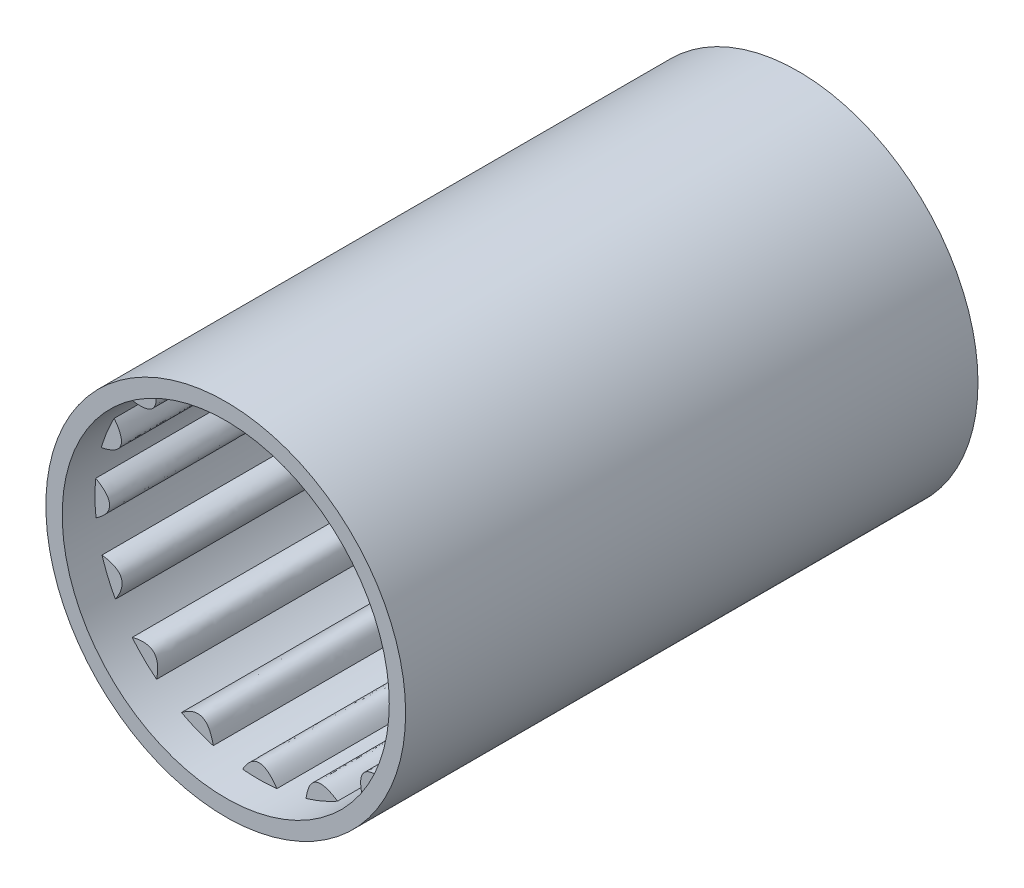
SolidWorks part; units mm, degrees
ref_plane "Front Plane" through (0, 0, 0) normal (0, 0, 1) x (1, 0, 0)
ref_plane "Top Plane" through (0, 0, 0) normal (0, 1, 0) x (1, 0, 0)
ref_plane "Right Plane" through (0, 0, 0) normal (1, 0, 0) x (0, 0, -1)
sketch "Sketch1" plane through (0, 0, 0) normal (0, 0, 1) x (1, 0, 0)
  circle A0 centre (0, 0) radius 11
  circle A1 centre (0, 0) radius 10
  dimension "D1" = 20
  dimension "22" = 22
extrude "Boss-Extrude1" add sketch "Sketch1" along normal blind 35
sketch "Sketch2" plane through (0, 0, 0) normal (0, 0, -1) x (-1, 0, 0)
  circle A0 centre (0, 0) radius 10 construction
  spline S0 degree 2 poles (-1.1281, -9.9362) (-0.0088, -8.2617) (0.9751, -9.9523) knots 0 0 0 1 1 1
  spline S1 degree 2 poles (-1.1281, -9.9362) (-0.0769, -10.0552) (0.9751, -9.9523) knots 0 0 0 1 1 1
  spline S2 degree 2 poles (-4.8446, -8.7481) (-3.1698, -7.6295) (-2.9077, -9.5679) knots 0 0 0 1 1 1
  spline S3 degree 2 poles (-4.8446, -8.7481) (-3.919, -9.2603) (-2.9077, -9.5679) knots 0 0 0 1 1 1
  spline S4 degree 2 poles (-7.8236, -6.2283) (-5.8482, -5.8357) (-6.3479, -7.7269) knots 0 0 0 1 1 1
  spline S5 degree 2 poles (-7.8236, -6.2283) (-7.1644, -7.0557) (-6.3479, -7.7269) knots 0 0 0 1 1 1
  spline S6 degree 2 poles (-9.6115, -2.7602) (-7.6362, -3.1535) (-8.8216, -4.7095) knots 0 0 0 1 1 1
  spline S7 degree 2 poles (-9.6115, -2.7602) (-9.3192, -3.7769) (-8.8216, -4.7095) knots 0 0 0 1 1 1
  spline S8 degree 2 poles (-9.9362, 1.1281) (-8.2617, 0.0088) (-9.9523, -0.9751) knots 0 0 0 1 1 1
  spline S9 degree 2 poles (-9.9362, 1.1281) (-10.0552, 0.0769) (-9.9523, -0.9751) knots 0 0 0 1 1 1
  spline S10 degree 2 poles (-8.7481, 4.8446) (-7.6295, 3.1698) (-9.5679, 2.9077) knots 0 0 0 1 1 1
  spline S11 degree 2 poles (-8.7481, 4.8446) (-9.2603, 3.919) (-9.5679, 2.9077) knots 0 0 0 1 1 1
  spline S12 degree 2 poles (-6.2283, 7.8236) (-5.8357, 5.8482) (-7.7269, 6.3479) knots 0 0 0 1 1 1
  spline S13 degree 2 poles (-6.2283, 7.8236) (-7.0557, 7.1644) (-7.7269, 6.3479) knots 0 0 0 1 1 1
  spline S14 degree 2 poles (-2.7602, 9.6115) (-3.1535, 7.6362) (-4.7095, 8.8216) knots 0 0 0 1 1 1
  spline S15 degree 2 poles (-2.7602, 9.6115) (-3.7769, 9.3192) (-4.7095, 8.8216) knots 0 0 0 1 1 1
  spline S16 degree 2 poles (1.1281, 9.9362) (0.0088, 8.2617) (-0.9751, 9.9523) knots 0 0 0 1 1 1
  spline S17 degree 2 poles (1.1281, 9.9362) (0.0769, 10.0552) (-0.9751, 9.9523) knots 0 0 0 1 1 1
  spline S18 degree 2 poles (4.8446, 8.7481) (3.1698, 7.6295) (2.9077, 9.5679) knots 0 0 0 1 1 1
  spline S19 degree 2 poles (4.8446, 8.7481) (3.919, 9.2603) (2.9077, 9.5679) knots 0 0 0 1 1 1
  spline S20 degree 2 poles (7.8236, 6.2283) (5.8482, 5.8357) (6.3479, 7.7269) knots 0 0 0 1 1 1
  spline S21 degree 2 poles (7.8236, 6.2283) (7.1644, 7.0557) (6.3479, 7.7269) knots 0 0 0 1 1 1
  spline S22 degree 2 poles (9.6115, 2.7602) (7.6362, 3.1535) (8.8216, 4.7095) knots 0 0 0 1 1 1
  spline S23 degree 2 poles (9.6115, 2.7602) (9.3192, 3.7769) (8.8216, 4.7095) knots 0 0 0 1 1 1
  spline S24 degree 2 poles (9.9362, -1.1281) (8.2617, -0.0088) (9.9523, 0.9751) knots 0 0 0 1 1 1
  spline S25 degree 2 poles (9.9362, -1.1281) (10.0552, -0.0769) (9.9523, 0.9751) knots 0 0 0 1 1 1
  spline S26 degree 2 poles (8.7481, -4.8446) (7.6295, -3.1698) (9.5679, -2.9077) knots 0 0 0 1 1 1
  spline S27 degree 2 poles (8.7481, -4.8446) (9.2603, -3.919) (9.5679, -2.9077) knots 0 0 0 1 1 1
  spline S28 degree 2 poles (6.2283, -7.8236) (5.8357, -5.8482) (7.7269, -6.3479) knots 0 0 0 1 1 1
  spline S29 degree 2 poles (6.2283, -7.8236) (7.0557, -7.1644) (7.7269, -6.3479) knots 0 0 0 1 1 1
  spline S30 degree 2 poles (2.7602, -9.6115) (3.1535, -7.6362) (4.7095, -8.8216) knots 0 0 0 1 1 1
  spline S31 degree 2 poles (2.7602, -9.6115) (3.7769, -9.3192) (4.7095, -8.8216) knots 0 0 0 1 1 1
  point P68 (0, 0)
extrude "Boss-Extrude2" add sketch "Sketch2" against normal blind 33 separate body
